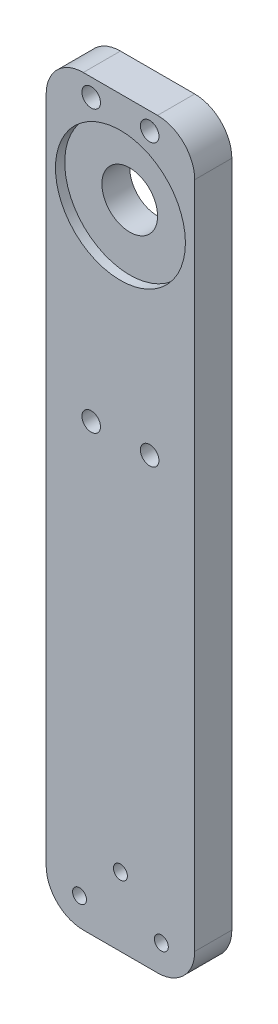
SolidWorks part; units mm, degrees
ref_plane "Front Plane" through (0, 0, 0) normal (0, 0, 1) x (1, 0, 0)
ref_plane "Top Plane" through (0, 0, 0) normal (0, 1, 0) x (1, 0, 0)
ref_plane "Right Plane" through (0, 0, 0) normal (1, 0, 0) x (0, 0, -1)
sketch "Sketch1" plane through (0, 0, 0) normal (0, 0, 1) x (1, 0, 0)
  line L1 (0, 0) -> (25.4, 0)
  line L2 (0, 0) -> (0, 127)
  line L3 (0, 127) -> (25.4, 127)
  line L4 (25.4, 0) -> (25.4, 127)
  dimension "D1" = 127
  dimension "D2" = 25.4
extrude "Boss-Extrude1" add sketch "Sketch1" along normal blind 6.35
sketch "Sketch2" plane through (0, 0, 6.35) normal (0, 0, 1) x (1, 0, 0)
  line L0 (0, 0) -> (25.4, 0) construction
  line L1 (0, 0) -> (25.4, 0) construction
  line L2 (5.7, 4.7625) -> (19.7, 4.7625) construction
  circle A0 centre (5.7, 4.7625) radius 1.1906
  circle A1 centre (19.7, 4.7625) radius 1.1906
  circle A2 centre (12.7, 11.7625) radius 1.1906
  point P4 (12.7, 4.7625)
  point P5 (12.7, 0)
  dimension "D3" = 2.3813
  dimension "D1" = 4.7625
  dimension "D2" = 14
  dimension "D4" = 7
extrude "Cut-Extrude1" cut sketch "Sketch2" against normal up to surface (6.35 mm away) up to face at (12.7, 63.5, 0)
fillet "Fillet1" radius 6.35 2 edges at (0, 0, 3.175) (25.4, 0, 3.175)
sketch "Sketch3" plane through (0, 0, 6.35) normal (0, 0, 1) x (1, 0, 0)
  line L0 (25.4, 127) -> (0, 127) construction
  line L1 (25.4, 127) -> (0, 127) construction
  circle A0 centre (12.7, 110.4999) radius 4.7625
  point P4 (12.7, 127)
  dimension "D2" = 9.525
  dimension "D1" = 16.5001
extrude "Cut-Extrude2" cut sketch "Sketch3" against normal up to surface (6.35 mm away) up to face at (4.5094, 4.7625, 0)
fillet "Fillet2" radius 6.35 2 edges at (0, 127, 3.175) (25.4, 127, 3.175)
sketch "Sketch4" plane through (0, 0, 6.35) normal (0, 0, 1) x (1, 0, 0)
  circle A0 centre (12.7, 110.4999) radius 11.1125
  dimension "D1" = 22.225
extrude "Cut-Extrude3" cut sketch "Sketch4" against normal blind 1.5875
sketch "Sketch5" plane through (0, 0, 6.35) normal (0, 0, 1) x (1, 0, 0)
  line L0 (19.05, 127) -> (6.35, 127) construction
  line L1 (19.05, 127) -> (6.35, 127) construction
  line L2 (7.7, 124) -> (17.7, 124) construction
  line L3 (7.7, 76) -> (17.7, 76) construction
  circle A0 centre (17.7, 124) radius 1.5875
  circle A1 centre (7.7, 124) radius 1.5875
  circle A2 centre (17.7, 76) radius 1.5875
  circle A3 centre (7.7, 76) radius 1.5875
  point P6 (12.7, 127)
  point P7 (12.7, 124)
  point P8 (12.7, 76)
  dimension "D4" = 3.175
  dimension "D1" = 3
  dimension "D2" = 51
  dimension "D3" = 10
extrude "Cut-Extrude4" cut sketch "Sketch5" against normal up to surface (6.35 mm away) up to face at (7.9375, 110.4999, 0)
